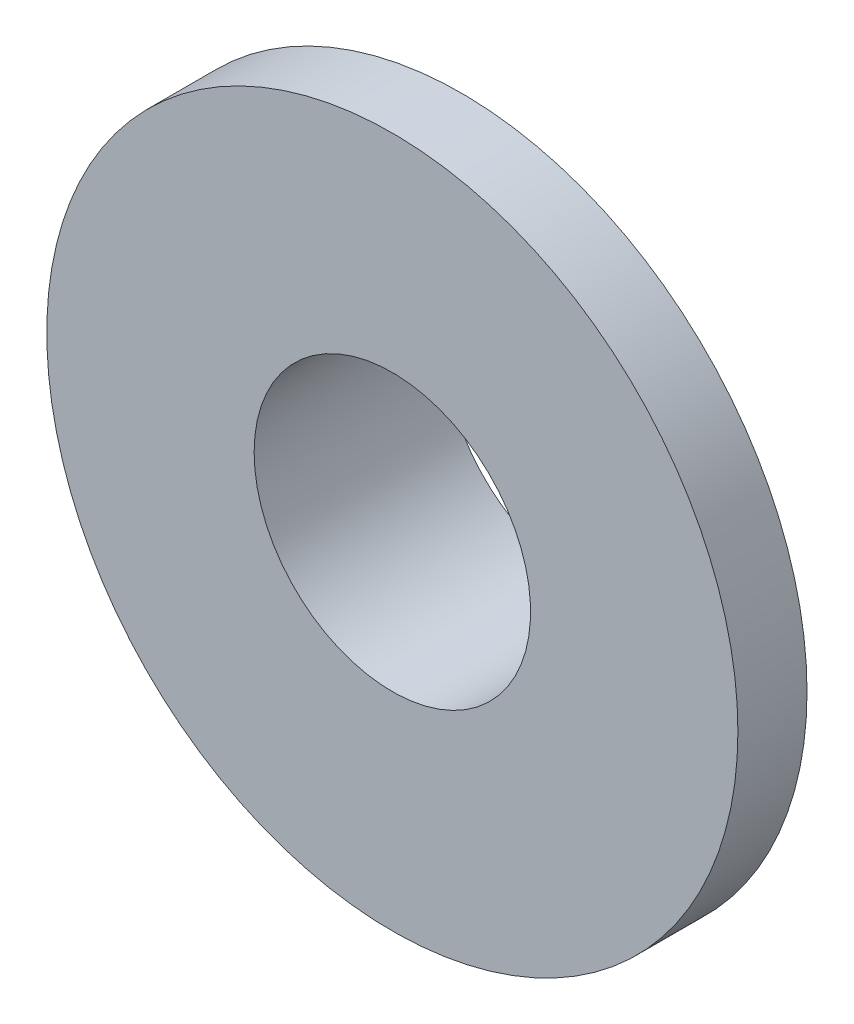
SolidWorks part; units mm, degrees
ref_plane "Front Plane" through (0, 0, 0) normal (0, 0, 1) x (1, 0, 0)
ref_plane "Top Plane" through (0, 0, 0) normal (0, 1, 0) x (1, 0, 0)
ref_plane "Right Plane" through (0, 0, 0) normal (1, 0, 0) x (0, 0, -1)
sketch "Sketch1" plane through (0, 0, 0) normal (0, 0, 1) x (1, 0, 0)
  circle A0 centre (0, 0) radius 10
  point P3 (0, 0)
  dimension "D1" = 20
extrude "Boss-Extrude1" add sketch "Sketch1" along normal blind 2
sketch "Sketch2" plane through (0, 0, 0) normal (0, 0, -1) x (-1, 0, 0)
  circle A0 centre (0, 0) radius 4.5
  dimension "D1" = 9
extrude "Boss-Extrude2" add sketch "Sketch2" along normal blind 3.5 contours A0
sketch "Sketch3" plane through (0, 0, -3.5) normal (0, 0, -1) x (-1, 0, 0)
  circle A0 centre (0, 0) radius 4
  dimension "D1" = 8
extrude "Cut-Extrude1" cut sketch "Sketch3" against normal through all
